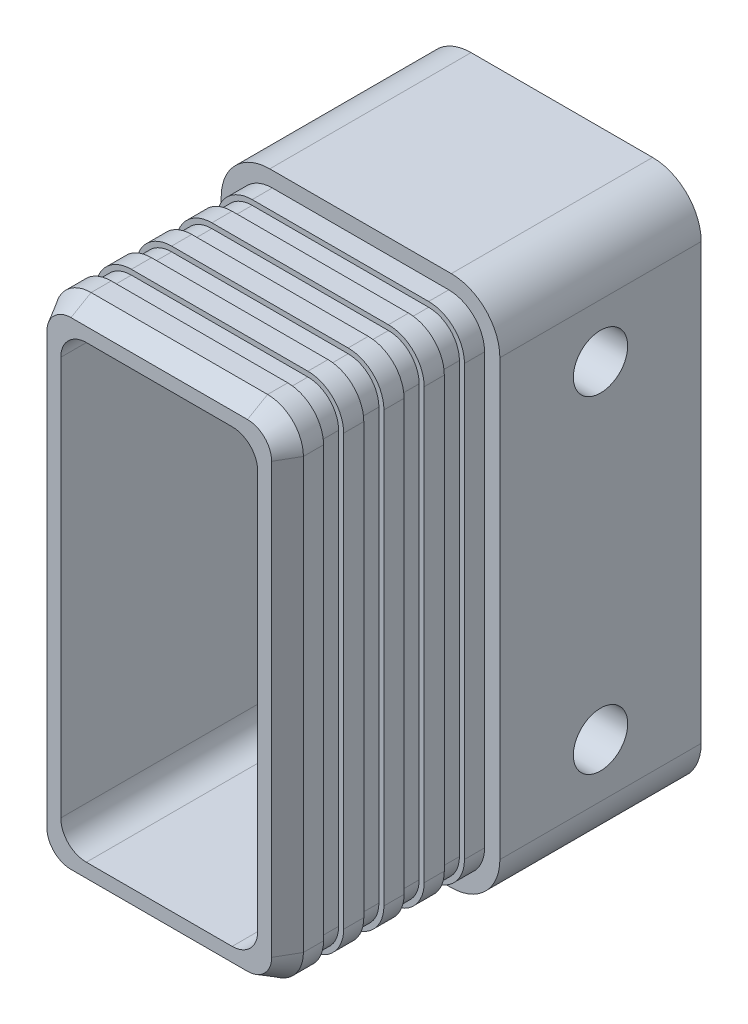
SolidWorks part; units mm, degrees
material "Nylon 101"
ref_plane "Front Plane" through (0, 0, 0) normal (0, 0, 1) x (1, 0, 0)
ref_plane "Top Plane" through (0, 0, 0) normal (0, 1, 0) x (1, 0, 0)
ref_plane "Right Plane" through (0, 0, 0) normal (1, 0, 0) x (0, 0, -1)
sketch "Sketch1" plane through (0, 0, 0) normal (0, 0, 1) x (1, 0, 0)
  line L1 (12.323, -24.896) -> (-12.323, -24.896)
  line L2 (12.323, -24.896) -> (12.323, 24.896)
  line L3 (12.323, 24.896) -> (-12.323, 24.896)
  line L4 (-12.323, -24.896) -> (-12.323, 24.896)
  line L5 (12.323, -24.896) -> (-12.323, 24.896) construction
  line L6 (12.323, 24.896) -> (-12.323, -24.896) construction
  point P0 (0, 0)
  dimension "D1" = 49.792
  dimension "D2" = 24.646
extrude "Boss-Extrude1" add sketch "Sketch1" along normal blind 20
sketch "Sketch2" plane through (0, 0, 0) normal (0, 0, 1) x (1, 0, 0)
  line L1 (13.843, -26.416) -> (-13.843, -26.416)
  line L2 (13.843, -26.416) -> (13.843, 26.416)
  line L3 (13.843, 26.416) -> (-13.843, 26.416)
  line L4 (-13.843, -26.416) -> (-13.843, 26.416)
  line L5 (13.843, -26.416) -> (-13.843, 26.416) construction
  line L6 (13.843, 26.416) -> (-13.843, -26.416) construction
  point P0 (0, 0)
  dimension "D1" = 52.832
  dimension "D2" = 27.686
extrude "Boss-Extrude2" add sketch "Sketch2" against normal blind 20
fillet "Fillet1" radius 3.556 4 edges at (-12.323, -24.896, 10) (12.323, -24.896, 10) (12.323, 24.896, 10) (-12.323, 24.896, 10)
fillet "Fillet2" radius 4.826 4 edges at (-13.843, 26.416, -10) (13.843, 26.416, -10) (13.843, -26.416, -10) (-13.843, -26.416, -10)
sketch "Sketch4" plane through (13.843, 0, 0) normal (1, 0, 0) x (0, 0, -1)
  line L0 (10, 26.416) -> (10, 16.256) construction
  line L1 (0, 26.416) -> (20, 26.416) construction
  line L2 (0, 18.0158) -> (10, 18.0158) construction
  line L4 (0, -21.34) -> (0, 21.34) construction
  line L5 (10, 16.0542) -> (20, 16.0542) construction
  line L6 (20, -21.59) -> (20, 21.59) construction
  line L7 (5.9262, 0) -> (-5.9262, 0) construction
  point P11 (10, 16.256)
  point P18 (10, -16.256)
  dimension "D1" = 10.16
hole_wizard "Ø5.0mm Dowel Hole2" positions "Sketch7" profile "Sketch8" hole size "Ø5.0" standard "ANSI Metric" end condition through all
sketch "Sketch7" plane through (13.843, 0, 0) normal (1, 0, 0) x (0, 0, -1)
  point P0 (10, 16.256)
  point P3 (10, -16.256)
sketch "Sketch8" plane through (13.843, 16.256, -10) normal (0, 1, 0) x (0, 0, -1)
  line L0 (0, 0) -> (0, 27.686)
  line L1 (0, 27.686) -> (2.7, 27.686)
  line L2 (2.7, 27.686) -> (2.7, 0)
  line L5 (2.7, 0) -> (0, 0)
  line L11 (0, -6.35) -> (0, 107.95) construction
  dimension "Thru Hole Dia." = 5.4
  dimension "Thru Hole Depth" = 27.686
sketch "Sketch9" plane through (0, 0, 20) normal (0, 0, 1) x (1, 0, 0)
  line L0 (8.767, 24.896) -> (-8.767, 24.896) construction
  line L1 (7.243, -22.356) -> (-7.243, -22.356)
  line L2 (9.783, -19.816) -> (9.783, 19.816)
  line L3 (7.243, 22.356) -> (-7.243, 22.356)
  line L4 (-9.783, -19.816) -> (-9.783, 19.816)
  line L5 (9.783, -22.356) -> (-9.783, 22.356) construction
  line L6 (9.783, 22.356) -> (-9.783, -22.356) construction
  line L7 (12.323, -21.34) -> (12.323, 21.34) construction
  arc A0 (7.243, -22.356) -> (9.783, -19.816) centre (7.243, -19.816) ccw
  arc A1 (-7.243, -22.356) -> (-9.783, -19.816) centre (-7.243, -19.816) cw
  arc A2 (-7.243, 22.356) -> (-9.783, 19.816) centre (-7.243, 19.816) ccw
  arc A3 (9.783, 19.816) -> (7.243, 22.356) centre (7.243, 19.816) ccw
  point P0 (0, 0)
  dimension "D3" = 2.54
  dimension "D1" = 2.54
  dimension "D2" = 2.54
extrude "Cut-Extrude1" cut sketch "Sketch9" against normal through all
sketch "Sketch10" plane through (0, 0, 20) normal (0, 0, 1) x (1, 0, 0)
  line L9 (-12.323, 21.34) -> (-12.323, -21.34)
  line L10 (-8.767, -24.896) -> (8.767, -24.896)
  line L11 (12.323, -21.34) -> (12.323, 21.34)
  line L12 (8.767, 24.896) -> (-8.767, 24.896)
  line L13 (-11.823, 21.34) -> (-11.823, -21.34)
  line L14 (-8.767, -24.396) -> (8.767, -24.396)
  line L15 (11.823, -21.34) -> (11.823, 21.34)
  line L16 (8.767, 24.396) -> (-8.767, 24.396)
  line L17 (-11.823, 21.34) -> (-11.823, -21.34)
  line L18 (-8.767, -24.396) -> (8.767, -24.396)
  line L19 (11.823, -21.34) -> (11.823, 21.34)
  line L20 (8.767, 24.396) -> (-8.767, 24.396)
  arc A8 (-8.767, 24.896) -> (-12.323, 21.34) centre (-8.767, 21.34) ccw
  arc A9 (-12.323, -21.34) -> (-8.767, -24.896) centre (-8.767, -21.34) ccw
  arc A10 (8.767, -24.896) -> (12.323, -21.34) centre (8.767, -21.34) ccw
  arc A11 (12.323, 21.34) -> (8.767, 24.896) centre (8.767, 21.34) ccw
  arc A12 (-11.823, -21.34) -> (-8.767, -24.396) centre (-8.767, -21.34) ccw
  arc A13 (8.767, -24.396) -> (11.823, -21.34) centre (8.767, -21.34) ccw
  arc A14 (11.823, 21.34) -> (8.767, 24.396) centre (8.767, 21.34) ccw
  arc A15 (-8.767, 24.396) -> (-11.823, 21.34) centre (-8.767, 21.34) ccw
  arc A16 (-11.823, -21.34) -> (-8.767, -24.396) centre (-8.767, -21.34) ccw
  arc A17 (8.767, -24.396) -> (11.823, -21.34) centre (8.767, -21.34) ccw
  arc A18 (11.823, 21.34) -> (8.767, 24.396) centre (8.767, 21.34) ccw
  arc A19 (-8.767, 24.396) -> (-11.823, 21.34) centre (-8.767, 21.34) ccw
  dimension "D1" = 0.5
extrude "Cut-Extrude2" cut sketch "Sketch10" against normal blind 2 from offset 4 offset against normal yes
pattern_linear "LPattern1" count 4 spacing 4 along (0, 0, -1) of "Cut-Extrude2"
chamfer "Chamfer1" distance 2 angle 30 8 edges at (12.323, 0, 20) (11.2815, 23.8545, 20) (11.2815, -23.8545, 20) (0, 24.896, 20) (0, -24.896, 20) (-11.2815, 23.8545, 20) (-11.2815, -23.8545, 20) (-12.323, 0, 20)
